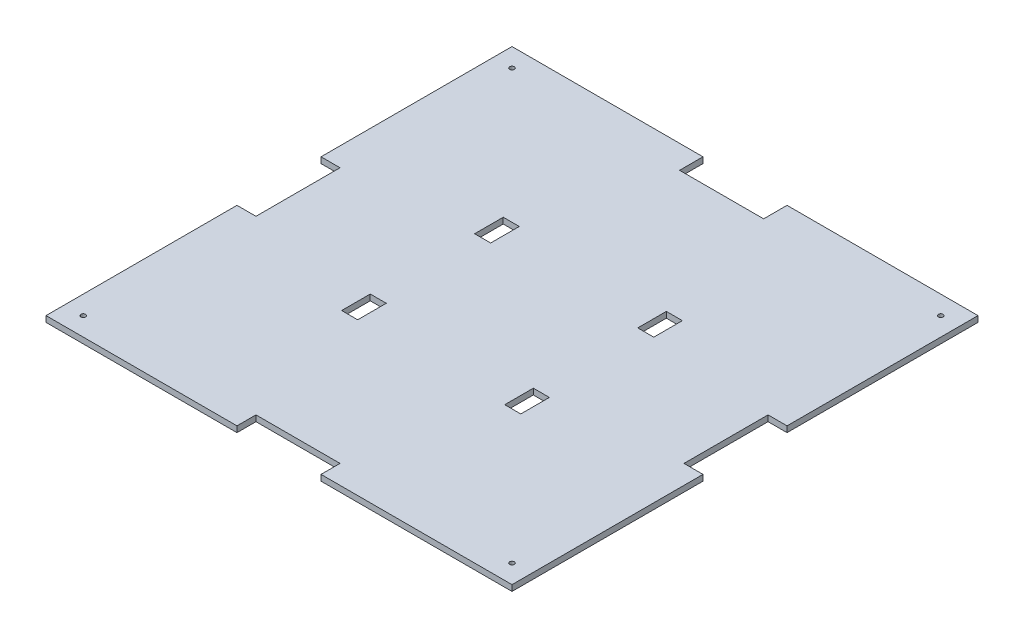
SolidWorks part; units mm, degrees
ref_plane "Front Plane" through (0, 0, 0) normal (0, 0, 1) x (1, 0, 0)
ref_plane "Top Plane" through (0, 0, 0) normal (0, 1, 0) x (1, 0, 0)
ref_plane "Right Plane" through (0, 0, 0) normal (1, 0, 0) x (0, 0, -1)
sketch "Sketch2" plane through (0, 0, 0) normal (0, 1, 0) x (1, 0, 0)
  line L1 (-125, -125) -> (125, -125)
  line L2 (-125, -125) -> (-125, 125)
  line L3 (-125, 125) -> (125, 125)
  line L4 (125, -125) -> (125, 125)
  line L5 (-125, -125) -> (125, 125) construction
  line L6 (-125, 125) -> (125, -125) construction
  point P0 (0, 0)
  dimension "D2" = 250
extrude "Base" add sketch "Sketch2" along normal blind 3.175
sketch "Sketch3" plane through (0, 3.175, 0) normal (0, 1, 0) x (1, 0, 0)
  line L0 (-125, 0) -> (125, 0) construction
  line L1 (-125, 125) -> (-125, -125) construction
  line L2 (125, -125) -> (125, 125) construction
  line L3 (-43.75, 125) -> (-43.75, -125) construction
  line L4 (125, 125) -> (-125, 125) construction
  line L5 (-125, -125) -> (125, -125) construction
  line L6 (0, 125) -> (0, -125) construction
  line L11 (-48.05, 28) -> (-39.45, 28)
  line L12 (-48.05, 28) -> (-48.05, 43.35)
  line L13 (-48.05, 43.35) -> (-39.45, 43.35)
  line L14 (-39.45, 28) -> (-39.45, 43.35)
  line L15 (-48.05, 28) -> (-39.45, 43.35) construction
  line L16 (-48.05, 43.35) -> (-39.45, 28) construction
  line L21 (-48.05, -43.35) -> (-39.45, -43.35)
  line L22 (-48.05, -43.35) -> (-48.05, -28)
  line L23 (-48.05, -28) -> (-39.45, -28)
  line L24 (-39.45, -43.35) -> (-39.45, -28)
  line L25 (-48.05, -43.35) -> (-39.45, -28) construction
  line L26 (-48.05, -28) -> (-39.45, -43.35) construction
  line L27 (48.05, -28) -> (39.45, -28)
  line L28 (39.45, -43.35) -> (39.45, -28)
  line L29 (48.05, -43.35) -> (39.45, -43.35)
  line L30 (48.05, -43.35) -> (48.05, -28)
  line L31 (48.05, 43.35) -> (39.45, 43.35)
  line L32 (39.45, 28) -> (39.45, 43.35)
  line L33 (48.05, 28) -> (39.45, 28)
  line L34 (48.05, 28) -> (48.05, 43.35)
  point P12 (-43.75, 35.675)
  point P17 (-43.75, -35.675)
  dimension "D1" = 43.75
  dimension "D2" = 8.6
  dimension "D3" = 15.35
  dimension "D4" = 56
  dimension "D5" = 28
extrude "Holes" cut sketch "Sketch3" against normal blind 10
sketch "Sketch4" plane through (0, 3.175, 0) normal (0, 1, 0) x (1, 0, 0)
  line L0 (0, 125) -> (0, -125) construction
  line L1 (125, 125) -> (-125, 125) construction
  line L2 (-125, -125) -> (125, -125) construction
  line L3 (-125, 0) -> (125, 0) construction
  line L4 (-125, 125) -> (-125, -125) construction
  line L5 (125, -125) -> (125, 125) construction
  line L7 (-22.55, 137.55) -> (22.55, 137.55)
  line L8 (-22.55, 137.55) -> (-22.55, 112.45)
  line L9 (-22.55, 112.45) -> (22.55, 112.45)
  line L10 (22.55, 137.55) -> (22.55, 112.45)
  line L11 (-22.55, 137.55) -> (22.55, 112.45) construction
  line L12 (-22.55, 112.45) -> (22.55, 137.55) construction
  line L41 (-114.8105, -22.55) -> (-135.1895, -22.55)
  line L42 (-114.8105, -22.55) -> (-114.8105, 22.55)
  line L43 (-114.8105, 22.55) -> (-135.1895, 22.55)
  line L44 (-135.1895, -22.55) -> (-135.1895, 22.55)
  line L45 (-114.8105, -22.55) -> (-135.1895, 22.55) construction
  line L46 (-114.8105, 22.55) -> (-135.1895, -22.55) construction
  line L47 (114.8105, -22.55) -> (135.1895, -22.55)
  line L48 (114.8105, -22.55) -> (114.8105, 22.55)
  line L49 (114.8105, 22.55) -> (135.1895, 22.55)
  line L50 (135.1895, -22.55) -> (135.1895, 22.55)
  line L51 (114.8105, -22.55) -> (135.1895, 22.55) construction
  line L52 (114.8105, 22.55) -> (135.1895, -22.55) construction
  line L53 (22.55, -114.8105) -> (-22.55, -114.8105)
  line L54 (22.55, -114.8105) -> (22.55, -135.1895)
  line L55 (22.55, -135.1895) -> (-22.55, -135.1895)
  line L56 (-22.55, -114.8105) -> (-22.55, -135.1895)
  line L57 (22.55, -114.8105) -> (-22.55, -135.1895) construction
  line L58 (22.55, -135.1895) -> (-22.55, -114.8105) construction
  point P31 (-25, 25)
  point P32 (25, -25)
  dimension "D1" = 25.1
  dimension "D2" = 45.1
extrude "Jigsaw" cut sketch "Sketch4" against normal blind 10
hole_wizard "Standoff Holes" positions "Sketch5" profile "Sketch6" tap size "M3" standard "ISO" end condition through all
sketch "Sketch5" plane through (0, 3.175, 0) normal (0, 1, 0) x (1, 0, 0)
  line L0 (-22.55, 125) -> (-125, 125) construction
  line L1 (-125, 125) -> (-125, 22.55) construction
  point P0 (-115, 115)
  dimension "D1" = 10
  dimension "D2" = 10
sketch "Sketch6" plane through (-115, 3.175, -115) normal (1, 0, 0) x (0, 0, 1)
  line L0 (0, 0) -> (0, 3.175)
  line L1 (0, 3.175) -> (1.25, 3.175)
  line L2 (1.25, 3.175) -> (1.25, 0)
  line L5 (1.25, 0) -> (0, 0)
  line L11 (0, -6.35) -> (0, 107.95) construction
  dimension "Thru Tap Drill Dia." = 2.5
  dimension "Thru Tap Drill Depth" = 3.175
cosmetic thread "Hole Thread9" parameters "D2"=3
hole_wizard "Standoff Holes 2" positions "Sketch7" profile "Sketch8" tap size "M3" standard "ISO" end condition through all
sketch "Sketch7" plane through (0, 3.175, 0) normal (0, 1, 0) x (1, 0, 0)
  line L0 (-125, -125) -> (-22.55, -125) construction
  line L1 (-125, -22.55) -> (-125, -125) construction
  line L2 (125, -125) -> (125, -22.55) construction
  line L3 (22.55, -125) -> (125, -125) construction
  line L4 (125, 22.55) -> (125, 125) construction
  line L5 (125, 125) -> (22.55, 125) construction
  point P0 (115, 115)
  point P2 (115, -115)
  point P4 (-115, -115)
  dimension "D1" = 10
  dimension "D2" = 10
  dimension "D3" = 10
  dimension "D4" = 10
  dimension "D5" = 10
  dimension "D6" = 10
sketch "Sketch8" plane through (115, 3.175, -115) normal (1, 0, 0) x (0, 0, 1)
  line L0 (0, 0) -> (0, 3.175)
  line L1 (0, 3.175) -> (1.25, 3.175)
  line L2 (1.25, 3.175) -> (1.25, 0)
  line L5 (1.25, 0) -> (0, 0)
  line L11 (0, -6.35) -> (0, 107.95) construction
  dimension "Thru Tap Drill Dia." = 2.5
  dimension "Thru Tap Drill Depth" = 3.175
cosmetic thread "Hole Thread11" parameters "D2"=3
cosmetic thread "Hole Thread12" parameters "D2"=3
cosmetic thread "Hole Thread15" parameters "D2"=3
